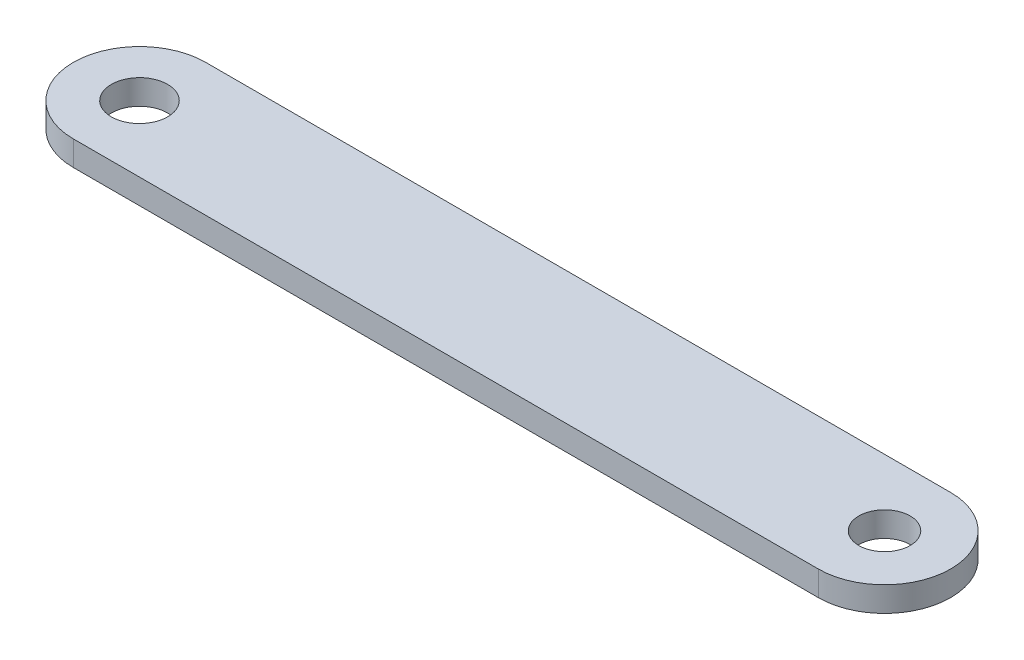
SolidWorks part; units mm, degrees
ref_plane "Front Plane" through (0, 0, 0) normal (0, 0, 1) x (1, 0, 0)
ref_plane "Top Plane" through (0, 0, 0) normal (0, 1, 0) x (1, 0, 0)
ref_plane "Right Plane" through (0, 0, 0) normal (1, 0, 0) x (0, 0, -1)
sketch "Sketch1" plane through (0, 0, 0) normal (0, 1, 0) x (1, 0, 0)
  line L0 (0, 0) -> (45, 0) construction
  line L1 (0, 4) -> (45, 4)
  line L2 (0, -4) -> (45, -4)
  arc A0 (0, 4) -> (0, -4) centre (0, 0) ccw
  arc A1 (45, -4) -> (45, 4) centre (45, 0) ccw
  point P3 (22.5, 0)
  dimension "D1" = 45
  dimension "D2" = 8
extrude "Boss-Extrude1" add sketch "Sketch1" along normal blind 1.5
hole_wizard "M3 Clearance Hole1" positions "Sketch3" profile "Sketch2" hole size "M3" standard "ANSI Metric" end condition through all
sketch "Sketch3" plane through (0, 1.5, 0) normal (0, 1, 0) x (1, 0, 0)
  point P0 (0, 0)
sketch "Sketch2" plane through (0, 1.5, 0) normal (1, 0, 0) x (0, 0, 1)
  line L0 (0, 0) -> (0, 1.5)
  line L1 (0, 1.5) -> (1.7, 1.5)
  line L2 (1.7, 1.5) -> (1.7, 0)
  line L5 (1.7, 0) -> (0, 0)
  line L11 (0, -6.35) -> (0, 107.95) construction
  dimension "Thru Hole Dia." = 3.4
  dimension "Thru Hole Depth" = 1.5
sketch "Sketch4" plane through (0, 1.5, 0) normal (0, 1, 0) x (1, 0, 0)
  circle A0 centre (45, 0) radius 1.55
  dimension "D1" = 3.1
extrude "Cut-Extrude1" cut sketch "Sketch4" against normal through all
